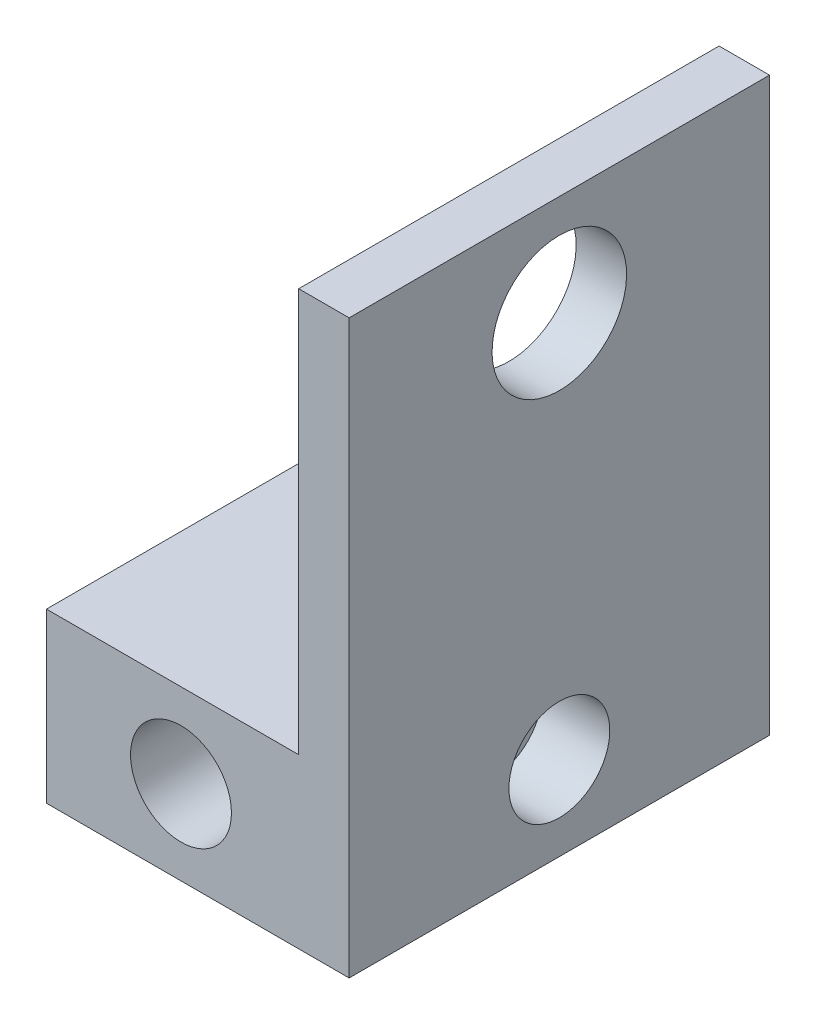
SolidWorks part; units mm, degrees
ref_plane "Plan de face" through (0, 0, 0) normal (0, 0, 1) x (1, 0, 0)
ref_plane "Plan de dessus" through (0, 0, 0) normal (0, 1, 0) x (1, 0, 0)
ref_plane "Plan de droite" through (0, 0, 0) normal (1, 0, 0) x (0, 0, -1)
sketch "Esquisse1" plane through (0, 0, 0) normal (0, 0, 1) x (1, 0, 0)
  line L1 (0, 0) -> (18, 0)
  line L2 (0, 0) -> (0, -34)
  line L3 (0, -34) -> (18, -34)
  line L4 (18, 0) -> (18, -34)
  dimension "D1" = 18
  dimension "D2" = 34
extrude "Boss.-Extru.1" add sketch "Esquisse1" along normal blind 25
sketch "Esquisse2" plane through (0, 0, 25) normal (0, 0, 1) x (1, 0, 0)
  line L0 (0, 0) -> (0, -34) construction
  line L2 (0, -34) -> (18, -34) construction
  line L4 (0, 0) -> (15, 0)
  line L5 (0, 0) -> (0, -24)
  line L6 (0, -24) -> (15, -24)
  line L7 (15, 0) -> (15, -24)
  circle A0 centre (8, -29) radius 3
  dimension "D1" = 6
  dimension "D2" = 8
  dimension "D3" = 5
  dimension "D4" = 5
  dimension "D5" = 15
extrude "Enlèv. mat.-Extru.1" cut sketch "Esquisse2" against normal through all
sketch "Esquisse3" plane through (18, 0, 0) normal (1, 0, 0) x (0, 0, -1)
  line L0 (-25, -34) -> (0, -34) construction
  line L1 (0, -34) -> (0, 0) construction
  circle A0 centre (-12.5, -29) radius 3
  dimension "D1" = 6
  dimension "D2" = 5
  dimension "D3" = 12.5
extrude "Enlèv. mat.-Extru.2" cut sketch "Esquisse3" against normal blind 4
sketch "Esquisse4" plane through (18, 0, 0) normal (1, 0, 0) x (0, 0, -1)
  line L1 (-25, -34) -> (0, -34) construction
  line L3 (-25, -34) -> (-25, 0) construction
  circle A0 centre (-12.5, -6) radius 4
  dimension "D1" = 8
  dimension "D2" = 28
  dimension "D3" = 12.5
extrude "Enlèv. mat.-Extru.3" cut sketch "Esquisse4" against normal through all
